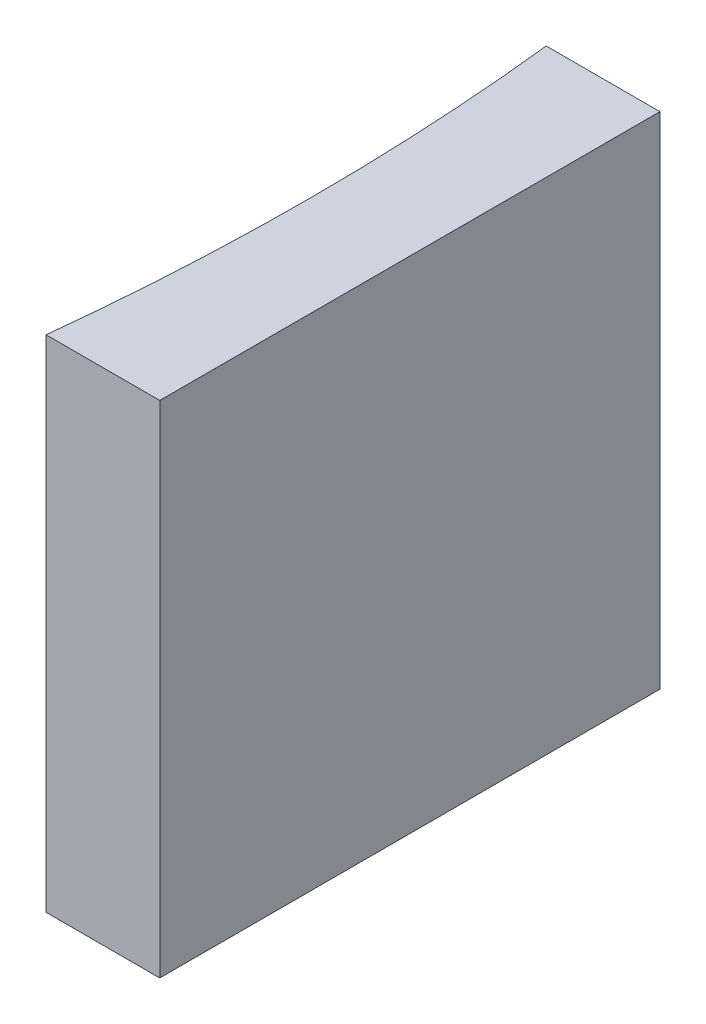
SolidWorks part; units mm, degrees
ref_plane "前视基准面" through (0, 0, 0) normal (0, 0, 1) x (1, 0, 0)
ref_plane "上视基准面" through (0, 0, 0) normal (0, 1, 0) x (1, 0, 0)
ref_plane "右视基准面" through (0, 0, 0) normal (1, 0, 0) x (0, 0, -1)
sketch "草图1" plane through (0, 0, 0) normal (0, 1, 0) x (1, 0, 0)
  line L0 (0, 0) -> (0, -10)
  line L1 (0, 0) -> (-2.2734, 0)
  line L2 (0, -10) -> (-2.2734, -10)
  line L3 (21.2259, -5) -> (-21.2259, -5) construction
  arc A0 (-2.2734, -10) -> (-2.2734, 0) centre (-47.85, -5) ccw
  point P7 (-2, -5)
  point P8 (0, -5)
  dimension "D2" = 45.85
  dimension "D3" = 2
  dimension "D1" = 10
extrude "凸台-拉伸1" add sketch "草图1" along normal blind 10
